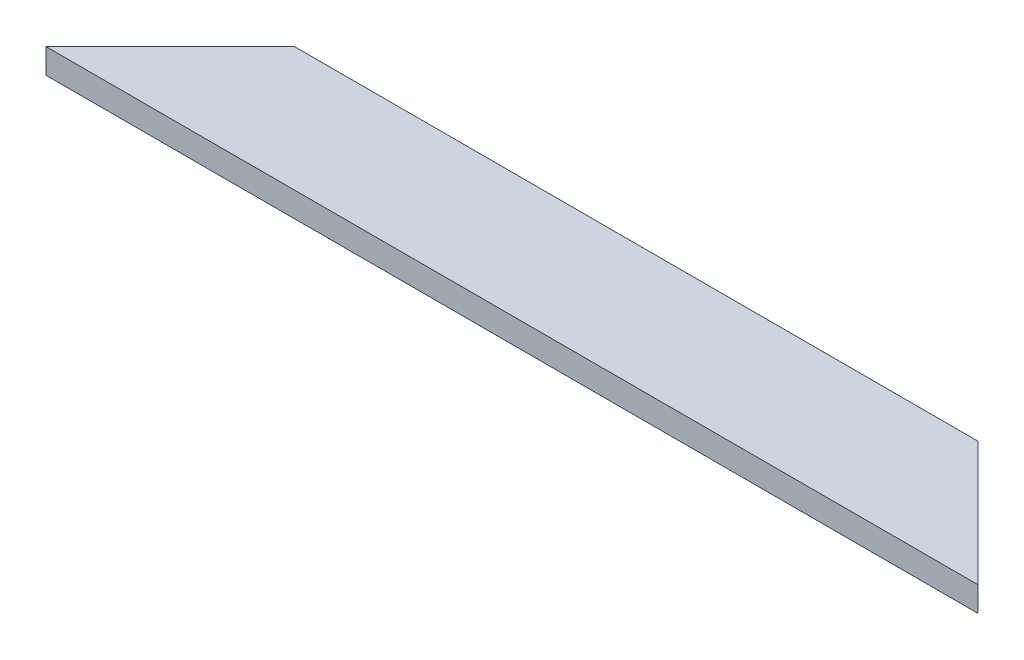
SolidWorks part; units mm, degrees
ref_plane "Спереди" through (0, 0, 0) normal (0, 0, 1) x (1, 0, 0)
ref_plane "Сверху" through (0, 0, 0) normal (0, 1, 0) x (1, 0, 0)
ref_plane "Справа" through (0, 0, 0) normal (1, 0, 0) x (0, 0, -1)
sketch "Эскиз1" plane through (0, 0, 0) normal (1, 0, 0) x (0, 0, -1)
  line L1 (0, 0) -> (20, 0)
  line L2 (0, 0) -> (0, 4)
  line L3 (0, 4) -> (20, 4)
  line L4 (20, 0) -> (20, 4)
extrude "Бобышка-Вытянуть1" add sketch "Эскиз1" along normal blind 150
sketch "Эскиз2" plane through (0, 4, 0) normal (0, 1, 0) x (1, 0, 0)
  line L0 (150, 0) -> (130, 20)
  line L1 (150, 20) -> (0, 20) construction
  line L2 (130, 20) -> (20, 20)
  line L3 (20, 20) -> (0, 0)
  line L4 (0, 0) -> (150, 0)
extrude "Вырез-Вытянуть1" cut sketch "Эскиз2" against normal blind 10 flip side to cut
